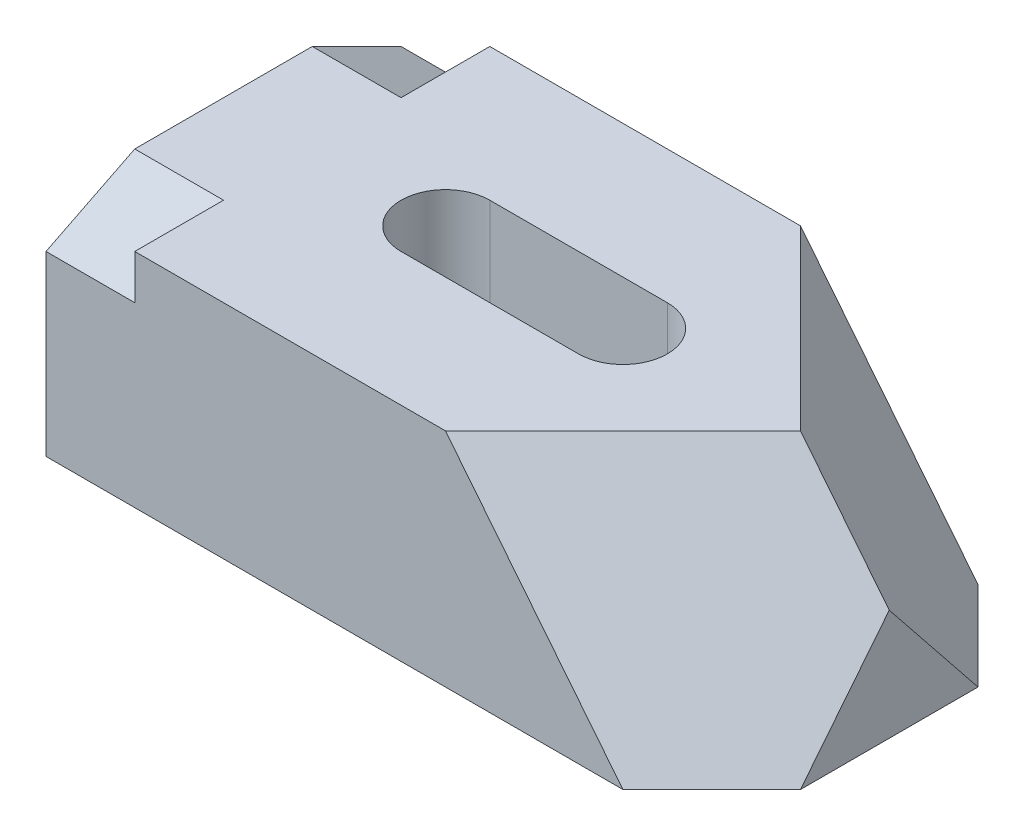
SolidWorks part; units mm, degrees
ref_plane "Front Plane" through (0, 0, 0) normal (0, 0, 1) x (1, 0, 0)
ref_plane "Top Plane" through (0, 0, 0) normal (0, 1, 0) x (1, 0, 0)
ref_plane "Right Plane" through (0, 0, 0) normal (1, 0, 0) x (0, 0, -1)
sketch "Sketch1" plane through (0, 0, 0) normal (0, 1, 0) x (1, 0, 0)
  line L1 (0, 0) -> (75, 0)
  line L2 (0, 0) -> (0, 40)
  line L3 (0, 40) -> (75, 40)
  line L4 (75, 0) -> (75, 40)
  dimension "D1" = 75
  dimension "D2" = 40
extrude "Boss-Extrude1" add sketch "Sketch1" along normal blind 25
sketch "Sketch2" plane through (0, 0, 0) normal (0, 0, 1) x (1, 0, 0)
  line L0 (75, 0) -> (65, 0) construction
  line L1 (0, 0) -> (75, 0) construction
  line L2 (75, 25) -> (45, 25) construction
  line L3 (0, 25) -> (75, 25) construction
  line L4 (65, 0) -> (45, 25)
  dimension "D1" = 10
  dimension "D2" = 30
sketch "Sketch3" plane through (75, 0, 0) normal (1, 0, 0) x (0, 0, -1)
  line L0 (0, 0) -> (10, 0) construction
  line L1 (0, 0) -> (40, 0) construction
  dimension "D1" = 10
sketch "Sketch4" plane through (0, 0, 0) normal (0, -1, 0) x (-1, 0, 0)
  line L0 (-65, 0) -> (-75, 10)
ref_plane "Plane1" through (24.6212, 19.697, 24.6212) normal (-0.6155, -0.4924, -0.6155) x (-0.4806, -0.3845, 0.7882)
sketch "Sketch5" plane through (24.6212, 19.697, 24.6212) normal (-0.6155, -0.4924, -0.6155) x (-0.4806, -0.3845, 0.7882)
  line L1 (-27.9152, -4.3284) -> (-84.8393, -4.3284)
  line L2 (-27.9152, -4.3284) -> (-27.9152, -54.1884)
  line L3 (-27.9152, -54.1884) -> (-84.8393, -54.1884)
  line L4 (-84.8393, -4.3284) -> (-84.8393, -54.1884)
extrude "Cut-Extrude1" cut sketch "Sketch5" against normal through all
sketch "Sketch7" plane through (0, 0, -40) normal (0, 0, -1) x (-1, 0, 0)
  line L0 (-65, 0) -> (-45, 25)
sketch "Sketch8" plane through (0, 0, 0) normal (0, -1, 0) x (-1, 0, 0)
  line L0 (-75, 40) -> (-75, 30) construction
  line L1 (-75, 10) -> (-75, 40) construction
  line L2 (-75, 30) -> (-65, 40)
  dimension "D1" = 10
ref_plane "Plane2" through (39.7727, 31.8182, -39.7727) normal (0.6155, 0.4924, -0.6155) x (-0.4806, -0.3845, -0.7882)
sketch "Sketch9" plane through (39.7727, 31.8182, -39.7727) normal (0.6155, 0.4924, -0.6155) x (-0.4806, -0.3845, -0.7882)
  line L1 (7.4379, -5.2899) -> (-58.7674, -5.2899)
  line L2 (7.4379, -5.2899) -> (7.4379, -63.2171)
  line L3 (7.4379, -63.2171) -> (-58.7674, -63.2171)
  line L4 (-58.7674, -5.2899) -> (-58.7674, -63.2171)
extrude "Cut-Extrude4" cut sketch "Sketch9" along normal through all
sketch "Sketch10" plane through (0, 0, 0) normal (-1, 0, 0) x (0, 0, 1)
  line L0 (-10, 25) -> (0, 20)
  line L1 (-40, 25) -> (0, 25) construction
  line L2 (0, 0) -> (0, 25) construction
  line L3 (0, 20) -> (0, 25)
  line L4 (0, 25) -> (-10, 25)
  dimension "D1" = 5
  dimension "D2" = 10
extrude "Cut-Extrude5" cut sketch "Sketch10" against normal blind 10
sketch "Sketch11" plane through (0, 0, 0) normal (-1, 0, 0) x (0, 0, 1)
  line L0 (-40, 20) -> (-30, 25)
  line L1 (-40, 0) -> (-40, 25) construction
  line L2 (-40, 25) -> (-10, 25) construction
  line L3 (-30, 25) -> (-40, 25)
  line L4 (-40, 25) -> (-40, 20)
  dimension "D1" = 5
  dimension "D2" = 10
extrude "Cut-Extrude6" cut sketch "Sketch11" against normal blind 10
sketch "Sketch12" plane through (0, 25, 0) normal (0, 1, 0) x (1, 0, 0)
  line L0 (0, 20) -> (25, 20) construction
  line L1 (0, 30) -> (0, 10) construction
  circle A0 centre (25, 20) radius 5
  dimension "D2" = 10
  dimension "D1" = 25
extrude "Cut-Extrude7" cut sketch "Sketch12" against normal through all
sketch "Sketch13" plane through (0, 25, 0) normal (0, 1, 0) x (1, 0, 0)
  line L0 (0, 20) -> (45, 20) construction
  line L1 (0, 30) -> (0, 10) construction
  circle A0 centre (45, 20) radius 5
  dimension "D2" = 10
  dimension "D1" = 45
extrude "Cut-Extrude8" cut sketch "Sketch13" against normal through all
sketch "Sketch14" plane through (0, 25, 0) normal (0, 1, 0) x (1, 0, 0)
  line L1 (45, 15) -> (25, 15)
  line L2 (45, 15) -> (45, 25)
  line L3 (45, 25) -> (25, 25)
  line L4 (25, 15) -> (25, 25)
  circle A0 centre (45, 20) radius 5 construction
  circle A1 centre (25, 20) radius 5 construction
extrude "Cut-Extrude9" cut sketch "Sketch14" against normal through all
